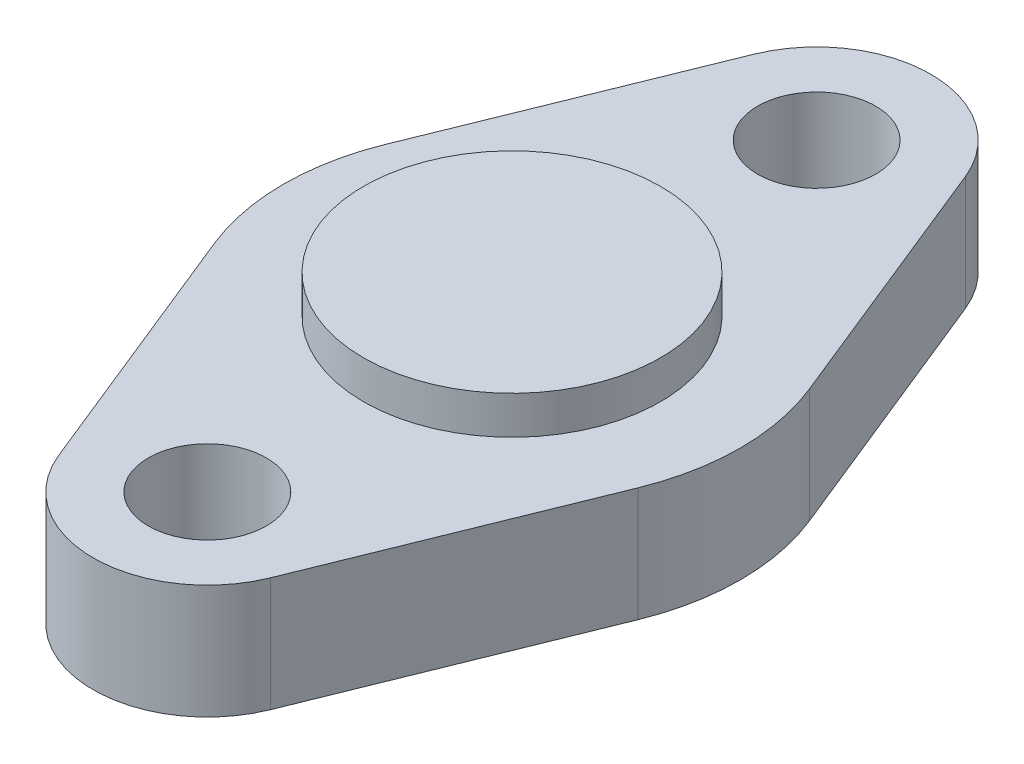
SolidWorks part; units mm, degrees
ref_plane "Alzado" through (0, 0, 0) normal (0, 0, 1) x (1, 0, 0)
ref_plane "Planta" through (0, 0, 0) normal (0, 1, 0) x (1, 0, 0)
ref_plane "Vista lateral" through (0, 0, 0) normal (1, 0, 0) x (0, 0, -1)
sketch "Croquis2" plane through (0, 0, 0) normal (0, 1, 0) x (1, 0, 0)
  line L0 (0, 0) -> (0, 16) construction
  line L1 (2.7811, 17.125) -> (5.5621, 10.25)
  line L2 (-2.7811, 17.125) -> (-5.5621, 10.25)
  line L3 (2.7811, -1.125) -> (5.5621, 5.75)
  line L4 (-2.7811, -1.125) -> (-5.5621, 5.75)
  arc A0 (0, 3) -> (-1.9111, 2.3125) centre (0, 0) ccw construction
  arc A1 (2.7811, 17.125) -> (-2.7811, 17.125) centre (0, 16) ccw
  arc A2 (-5.5621, 10.25) -> (5.5621, 5.75) centre (0, 8) ccw construction
  circle A3 centre (0, 16) radius 1.55
  circle A4 centre (0, 0) radius 1.55
  arc A5 (5.5621, 5.75) -> (5.5621, 10.25) centre (0, 8) ccw
  arc A6 (-2.7811, -1.125) -> (2.7811, -1.125) centre (0, 0) ccw
  arc A7 (-5.5621, 10.25) -> (-5.5621, 5.75) centre (0, 8) ccw
  arc A8 (5.5621, 5.75) -> (5.5621, 10.25) centre (0, 8) ccw
  arc A9 (-1.9111, 2.3125) -> (0, 2) centre (0, 8) ccw
  dimension "D1" = 6
  dimension "D3" = 12
  dimension "D4" = 3.1
  dimension "D2" = 16
extrude "Saliente-Extruir1" add sketch "Croquis2" along normal blind 3
sketch "Croquis3" plane through (0, 3, 0) normal (0, 1, 0) x (1, 0, 0)
  line L0 (0, 16) -> (0, 0) construction
  circle A6 centre (0, 8) radius 3.9
  dimension "D1" = 7.8
extrude "Saliente-Extruir2" add sketch "Croquis3" along normal blind 1
